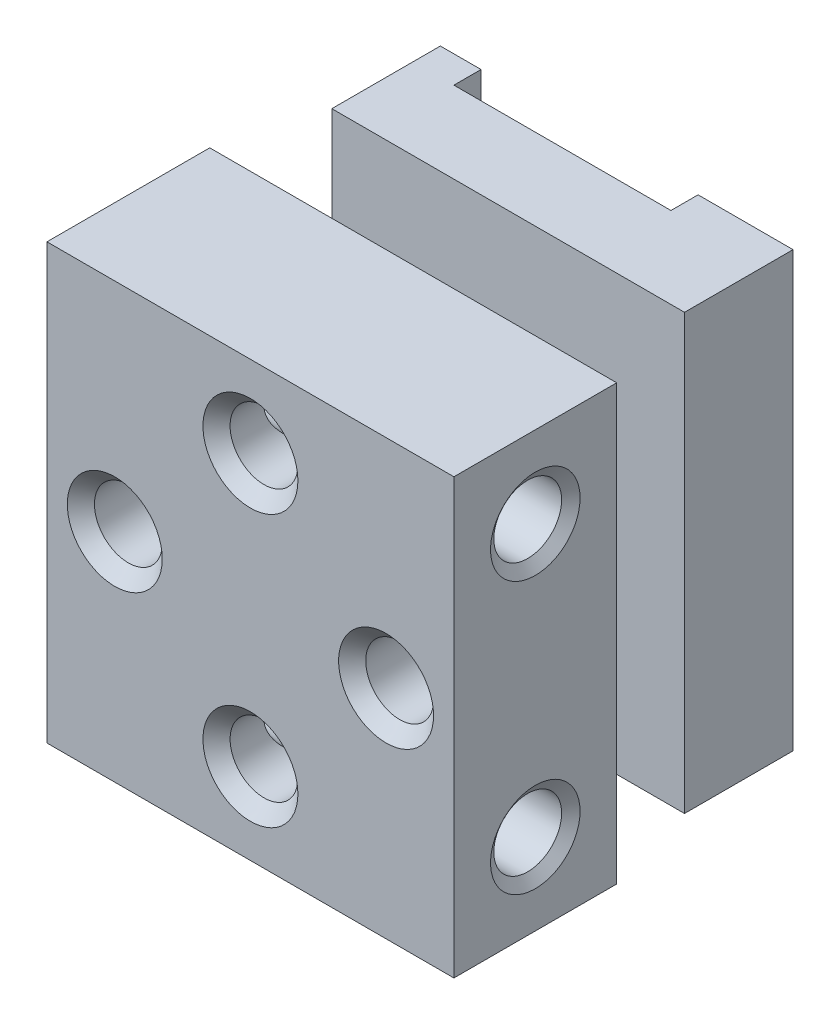
SolidWorks part; units mm, degrees
material "2024-T4"
ref_plane "Спереди" through (0, 0, 0) normal (0, 0, 1) x (1, 0, 0)
ref_plane "Сверху" through (0, 0, 0) normal (0, 1, 0) x (1, 0, 0)
ref_plane "Справа" through (0, 0, 0) normal (1, 0, 0) x (0, 0, -1)
sketch "Эскиз1" plane through (0, 0, 0) normal (0, 0, 1) x (1, 0, 0)
  line L0 (-7.5, 8) -> (7.5, -8) construction
  line L1 (-7.5, 8) -> (7.5, 8)
  line L2 (-7.5, 8) -> (-7.5, -8)
  line L3 (-7.5, -8) -> (7.5, -8)
  line L4 (7.5, 8) -> (7.5, -8)
  line L5 (7.5, 8) -> (-7.5, -8) construction
  point P5 (0, 0)
  dimension "D1" = 15
  dimension "D2" = 16
extrude "Вытянуть1" add sketch "Эскиз1" along normal blind 13.5
sketch "Эскиз2" plane through (0, 0, 0) normal (0, 0, -1) x (-1, 0, 0)
  line L0 (6.5, 8) -> (6.5, -8)
  line L1 (-7.5, 8) -> (7.5, 8) construction
  line L2 (7.5, -8) -> (-7.5, -8) construction
  line L3 (-6.5, 8) -> (-6.5, -8)
  line L4 (-7.5, -8) -> (-7.5, 8) construction
  line M1 (7.5, -8) -> (7.5, 8)
  line M2 (7.5, 8) -> (-7.5, 8)
  line M3 (-7.5, 8) -> (-7.5, -8)
  line M4 (-7.5, -8) -> (7.5, -8)
  dimension "D1" = 1
  dimension "D2" = 1
extrude "Вырез-Вытянуть2" cut sketch "Эскиз2" against normal blind 7.5 contours L0 M4 M1 M2 | L3 M2 M3 M4
sketch "Эскиз4" plane through (-6.5, 0, 0) normal (-1, 0, 0) x (0, 0, 1)
  line L0 (7.5, 8) -> (7.5, 3)
  line L1 (7.5, -8) -> (7.5, 8) construction
  line L2 (7.5, 3) -> (4, 3)
  line L3 (0, -8) -> (0, 8) construction
  line L4 (4, 3) -> (4, 8)
  line L5 (13.5, 0) -> (0, 0) construction
  line L6 (13.5, 8) -> (13.5, -8) construction
  line L7 (4, -3) -> (4, -8)
  line L8 (7.5, -3) -> (4, -3)
  line L9 (7.5, -8) -> (7.5, -3)
  line L10 (7.5, 8) -> (0, 8) construction
  line M2 (0, -8) -> (7.5, -8)
  line M3 (7.5, -8) -> (7.5, 8)
  line M4 (7.5, 8) -> (0, 8)
  dimension "D1" = 3
  dimension "D2" = 3.5
extrude "Вырез-Вытянуть4" cut sketch "Эскиз4" against normal through all contours L4 L2 M4 M3 | L8 L7 M2 M3
sketch "Эскиз5" plane through (0, 3, 0) normal (0, 1, 0) x (-1, 0, 0)
  line L0 (-7.5, 7.5) -> (-3, 7.5)
  line L1 (7.5, 7.5) -> (-7.5, 7.5) construction
  line L2 (-3, 7.5) -> (-3, 4)
  line L3 (-6.5, 4) -> (6.5, 4) construction
  line L4 (-3, 4) -> (-6.5, 4)
  line L5 (0, 4) -> (0, 13.5) construction
  line L6 (3, 4) -> (6.5, 4)
  line L7 (3, 7.5) -> (3, 4)
  line L8 (7.5, 7.5) -> (3, 7.5)
  line L9 (-7.5, 13.5) -> (7.5, 13.5) construction
  line L10 (-6.5, 4) -> (-6.5, 7.5) construction
  dimension "D1" = 3
extrude "Вырез-Вытянуть9" cut sketch "Эскиз5" against normal up to next (6 mm away) from surface at 0
sketch "Эскиз6" plane through (0, 3, 0) normal (0, 1, 0) x (-1, 0, 0)
  line L0 (-3, 6.5) -> (-0.5, 6.5)
  line L1 (-3, 7.5) -> (-3, 4) construction
  line L2 (-0.5, 6.5) -> (-0.5, 7.5)
  line L3 (7.5, 7.5) -> (-7.5, 7.5) construction
  line L4 (-0.5, 7.5) -> (-3, 7.5)
  line L5 (3, 4) -> (3, 7.5) construction
  line L7 (0.5, 7.5) -> (29.3, 7.5)
  line L8 (0.5, 6.5) -> (0.5, 7.5)
  line L9 (3, 6.5) -> (0.5, 6.5)
  line M2 (3, 4) -> (3, 7.5)
  line M3 (3, 7.5) -> (-3, 7.5)
  line M4 (-3, 7.5) -> (-3, 4)
  dimension "D1" = 1
  dimension "D2" = 1
extrude "Вырез-Вытянуть10" cut sketch "Эскиз6" against normal up to next contours L0 L2 M3 M4 | L9 L8 M2 M3
sketch "Эскиз7" plane through (3, 0, 0) normal (1, 0, 0) x (0, 0, -1)
  line L0 (-5, 3) -> (-5, 0.5)
  line L1 (-6.5, 3) -> (-4, 3) construction
  line L2 (-5, 0.5) -> (-4, 0.5)
  line L3 (-4, 8) -> (-4, -8) construction
  line L4 (-4, 0.5) -> (-4, 3)
  line L5 (-7, 0) -> (-4, 0) construction
  line L7 (-4, -0.5) -> (-4, -3)
  line L8 (-5, -0.5) -> (-4, -0.5)
  line L9 (-5, -3) -> (-5, -0.5)
  line M2 (-6.5, -3) -> (-4, -3)
  line M3 (-4, -3) -> (-4, 3)
  line M4 (-4, 3) -> (-6.5, 3)
  dimension "D1" = 1
  dimension "D2" = 2.5
extrude "Вырез-Вытянуть11" cut sketch "Эскиз7" against normal through all contours L0 L2 M3 M4 | L9 L8 M2 M3
sketch "Эскиз8" plane through (0, 8, 0) normal (0, 1, 0) x (-1, 0, 0)
  line L0 (5, 0) -> (5, 1)
  line L1 (-6.5, 0) -> (6.5, 0) construction
  line L2 (5, 1) -> (-3, 1)
  line L3 (-3, 1) -> (-3, 0)
  line L5 (6.5, 4) -> (6.5, 0) construction
  line M4 (-6.5, 0) -> (6.5, 0)
  dimension "D1" = 8
  dimension "D2" = 1.5
  dimension "D3" = 1
extrude "Вырез-Вытянуть12" cut sketch "Эскиз8" against normal through all contours L3 L0 L2 M4
hole_wizard "Отверстие обработанное метчиком M31" positions "Трехмерный эскиз1" profile "Эскиз9" tap size "M3" standard "DIN" end condition up to next
sketch3d "Трехмерный эскиз1"
  line L0 (-7.5, 8, 13.5) -> (-7.5, -8, 13.5) construction
  line L1 (-7.5, -8, 13.5) -> (7.5, -8, 13.5) construction
  point P0 (0, -5, 13.5)
  point P2 (0, 5, 13.5)
  point P4 (5, 0, 13.5)
  point P6 (-5, 0, 13.5)
  dimension "D1" = 2.5
  dimension "D2" = 10
  dimension "D3" = 10
  dimension "D4" = 3
  dimension "D5" = 8
  dimension "D6" = 7.5
sketch "Эскиз9" plane through (0, -5, 13.5) normal (1, 0, 0) x (0, -1, 0)
  line L0 (0, 0) -> (0, 6)
  line L1 (0, 6) -> (1.75, 6)
  line L2 (1.25, 5.5) -> (1.25, 0.5)
  line L3 (1.25, 0.5) -> (1.75, 0)
  line L5 (1.75, 0) -> (0, 0)
  line L6 (-1.25, 0.5) -> (-1.75, 0) construction
  line L7 (1.75, 6) -> (1.25, 5.5)
  line L8 (-1.75, 6) -> (-1.25, 5.5) construction
  line L11 (0, -6.35) -> (0, 107.95) construction
  dimension "Диаметр проходного сверла" = 2.5
  dimension "Глубина проходного сверла" = 6
  dimension "Диаметр передней зенковки" = 3.5
  dimension "Угол передней зенковки" = 90
  dimension "Диаметр задней зенковки" = 3.5
  dimension "Угол задней зенковки" = 90
cosmetic thread "Отверстие резьбы5" parameters "D2"=3
cosmetic thread "Отверстие резьбы6" parameters "D2"=3
cosmetic thread "Отверстие резьбы7" parameters "D2"=3
cosmetic thread "Отверстие резьбы8" parameters "D2"=3
hole_wizard "Отверстие обработанное метчиком M33" positions "Трехмерный эскиз2" profile "Эскиз10" tap size "M3" standard "DIN"
sketch3d "Трехмерный эскиз2"
  line L0 (-7.5, 8, 13.5) -> (-7.5, 8, 7.5) construction
  line L1 (-7.5, -8, 13.5) -> (-7.5, -8, 7.5) construction
  line L2 (-7.5, 8, 13.5) -> (-7.5, -8, 13.5) construction
  point P0 (-7.5, 5, 10.5)
  point P2 (-7.5, -5, 10.5)
  dimension "D1" = 3
  dimension "D2" = 3
  dimension "D3" = 3
sketch "Эскиз10" plane through (-7.5, 5, 10.5) normal (0, 1, 0) x (0, 0, 1)
  line L0 (0, 0) -> (0, 8.2511)
  line L1 (0, 8.2511) -> (1.25, 7.5)
  line L2 (1.25, 7.5) -> (1.25, 0.2801)
  line L3 (1.25, 0.2801) -> (1.65, 0)
  line L5 (1.65, 0) -> (0, 0)
  line L6 (-1.25, 0.2801) -> (-1.65, 0) construction
  line L10 (0, 8.2511) -> (-1.25, 7.5) construction
  line L11 (0, -6.35) -> (0, 107.95) construction
  dimension "Диаметр сверла" = 2.5
  dimension "Глубина сверла" = 7.5
  dimension "Диаметр передней зенковки" = 3.3
  dimension "Угол передней зенковки" = 110
  dimension "Угол заточки сверла" = 118
cosmetic thread "Отверстие резьбы1" parameters "D1"=5, "D2"=3
cosmetic thread "Отверстие резьбы2" parameters "D1"=5, "D2"=3
sketch "Эскиз11" plane through (0, 0, 0) normal (0, 1, 0) x (1, 0, 0)
  line L0 (10.5, -4) -> (10.5, -7.5)
  line L1 (10.5, -4) -> (3, -4)
  line L2 (3, -4) -> (3, -7.5)
  line L4 (3, -7.5) -> (10.5, -7.5)
  line L10 (0, 0) -> (0, -13.5) construction
  line L11 (7.5, -13.5) -> (-7.5, -13.5) construction
  dimension "D1" = 6
revolve "Вырез-Повернуть1" cut sketch "Эскиз11" angle 360 about L10
hole_wizard "Отверстие обработанное метчиком M35" positions "Эскиз13" profile "Эскиз12" tap size "M3" standard "DIN"
sketch "Эскиз13" plane through (7.5, 6.8676, -0.6511) normal (1, 0, 0) x (0, 0, -1)
  point P1 (-11.1511, -1.8676)
  point P4 (-11.1511, -11.8676)
sketch "Эскиз12" plane through (7.5, 5, 10.5) normal (0, 1, 0) x (0, 0, -1)
  line L0 (0, 0) -> (0, 8.2511)
  line L1 (0, 8.2511) -> (1.25, 7.5)
  line L2 (1.25, 7.5) -> (1.25, 0.2801)
  line L3 (1.25, 0.2801) -> (1.65, 0)
  line L5 (1.65, 0) -> (0, 0)
  line L6 (-1.25, 0.2801) -> (-1.65, 0) construction
  line L10 (0, 8.2511) -> (-1.25, 7.5) construction
  line L11 (0, -6.35) -> (0, 107.95) construction
  dimension "Диаметр сверла" = 2.5
  dimension "Глубина сверла" = 7.5
  dimension "Диаметр передней зенковки" = 3.3
  dimension "Угол передней зенковки" = 110
  dimension "Угол заточки сверла" = 118
cosmetic thread "Отверстие резьбы3" parameters "D1"=5, "D2"=3
cosmetic thread "Отверстие резьбы4" parameters "D1"=5, "D2"=3
